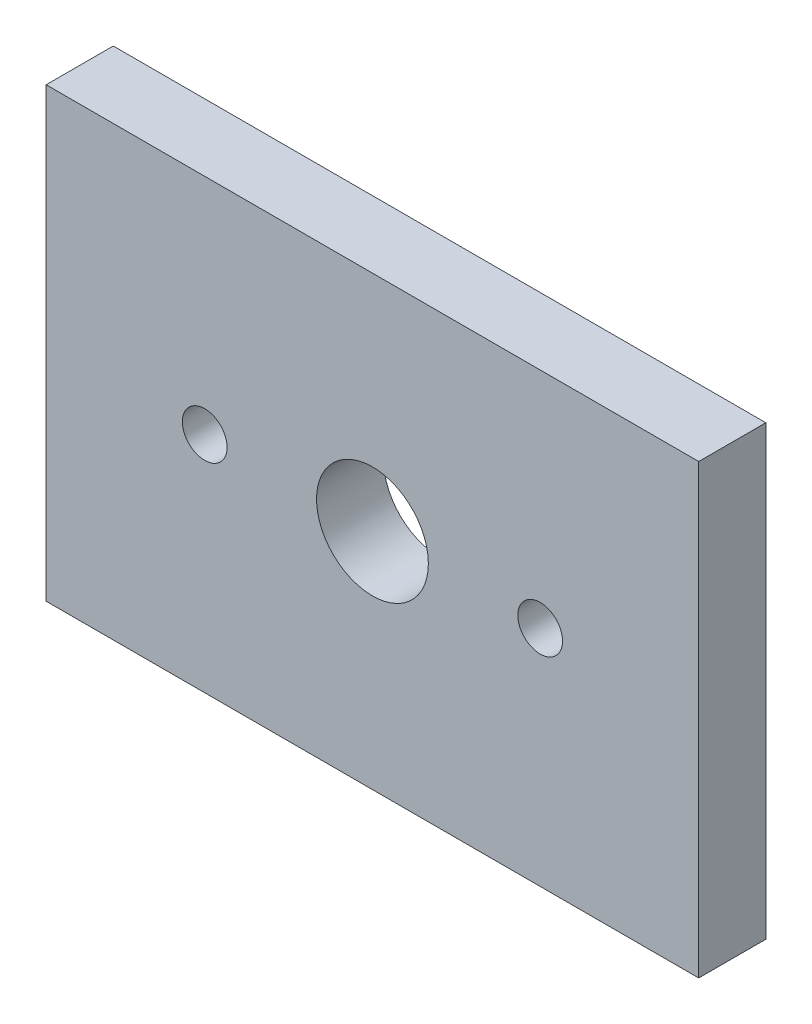
SolidWorks part; units mm, degrees
ref_plane "前基準面" through (0, 0, 0) normal (0, 0, 1) x (1, 0, 0)
ref_plane "上基準面" through (0, 0, 0) normal (0, 1, 0) x (1, 0, 0)
ref_plane "右基準面" through (0, 0, 0) normal (1, 0, 0) x (0, 0, -1)
sketch "草圖1" plane through (0, 0, 0) normal (0, 0, 1) x (1, 0, 0)
  line L1 (-6.0957, 13.6411) -> (23.082, 13.6411)
  line L2 (-6.0957, 13.6411) -> (-6.0957, -6.3589)
  line L3 (-6.0957, -6.3589) -> (23.082, -6.3589)
  line L4 (23.082, 13.6411) -> (23.082, -6.3589)
extrude "填料-伸長1" add sketch "草圖1" along normal blind 3
sketch "草圖2" plane through (0, 0, 0) normal (0, 0, 1) x (1, 0, 0)
  line L0 (23.082, 3.6411) -> (-6.0957, 3.6411) construction
  line L1 (23.082, -6.3589) -> (23.082, 13.6411) construction
  line L2 (-6.0957, 13.6411) -> (-6.0957, -6.3589) construction
  line L3 (8.4932, 13.6411) -> (8.4932, -6.3589) construction
  line L4 (23.082, 13.6411) -> (-6.0957, 13.6411) construction
  line L5 (-6.0957, -6.3589) -> (23.082, -6.3589) construction
  circle A0 centre (8.4932, 3.6411) radius 2.5
  circle A1 centre (15.9932, 3.6411) radius 1
  circle A2 centre (0.9932, 3.6411) radius 1
  dimension "D2" = 2
  dimension "D3" = 5
  dimension "D1" = 7.5
sketch "Sketch2" plane through (0, 0, 0) normal (0, 0, 1) x (1, 0, 0)
  line L0 (8.4932, 13.6411) -> (8.4932, -6.3589) construction
  circle A0 centre (15.9932, 3.6411) radius 2
  circle A1 centre (0.9932, 3.6411) radius 2
  dimension "D1" = 4
extrude "Boss-Extrude3" add sketch "Sketch2" against normal blind 3
extrude "Cut-Extrude1" cut sketch "草圖2" against normal blind 6 and the other way blind 10
